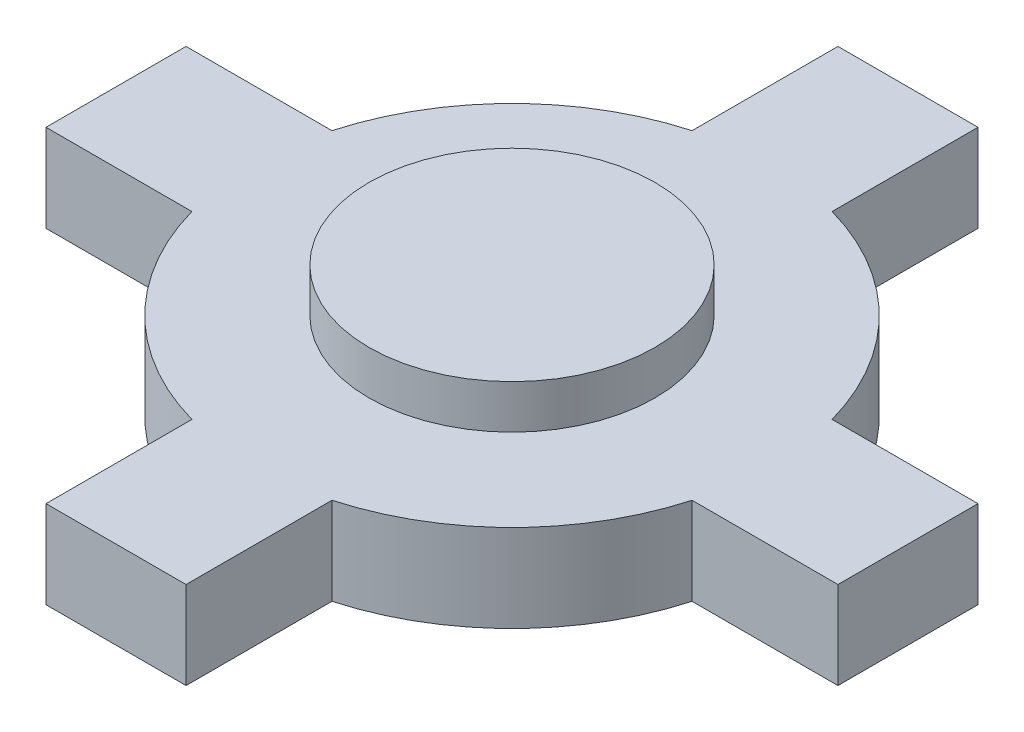
SolidWorks part; units mm, degrees
ref_plane "前视基准面" through (0, 0, 0) normal (0, 0, 1) x (1, 0, 0)
ref_plane "上视基准面" through (0, 0, 0) normal (0, 1, 0) x (1, 0, 0)
ref_plane "右视基准面" through (0, 0, 0) normal (1, 0, 0) x (0, 0, -1)
other "Configuration Table"
sketch "草图1" plane through (0, 0, 0) normal (0, 1, 0) x (1, 0, 0)
  line L0 (0, 7.9747) -> (0, -8.6444) construction
  line L1 (-13.5703, 2.4) -> (-8.5703, 2.4)
  line L2 (-13.5703, 2.4) -> (-13.5703, -2.4)
  line L3 (-13.5703, -2.4) -> (-8.5703, -2.4)
  line L4 (13.5703, 2.4) -> (13.5703, -2.4)
  line L5 (-2.4, 13.5703) -> (2.4, 13.5703)
  line L6 (-2.4, 13.5703) -> (-2.4, 8.5703)
  line L7 (-2.4, -13.5703) -> (2.4, -13.5703)
  line L8 (2.4, 13.5703) -> (2.4, 8.5703)
  line L13 (-10.8789, 0) -> (11.1113, 0) construction
  line L15 (-2.4, -8.5703) -> (-2.4, -13.5703)
  line L16 (8.5703, 2.4) -> (13.5703, 2.4)
  line L17 (8.5703, -2.4) -> (13.5703, -2.4)
  line L18 (2.4, -8.5703) -> (2.4, -13.5703)
  arc A0 (-2.4, 8.5703) -> (-8.5703, 2.4) centre (0, 0) ccw
  arc A1 (8.5703, 2.4) -> (2.4, 8.5703) centre (0, 0) ccw
  arc A2 (2.4, -8.5703) -> (8.5703, -2.4) centre (0, 0) ccw
  arc A3 (-8.5703, -2.4) -> (-2.4, -8.5703) centre (0, 0) ccw
  dimension "D1" = 17.8
  dimension "D2" = 4.8
  dimension "D3" = 5
extrude "凸台-拉伸1" add sketch "草图1" along normal blind 3
sketch "草图2" plane through (0, 3, 0) normal (0, 1, 0) x (1, 0, 0)
  circle A0 centre (0, 0) radius 4.9
  dimension "D1" = 9.8
extrude "凸台-拉伸2" add sketch "草图2" along normal blind 1.5
